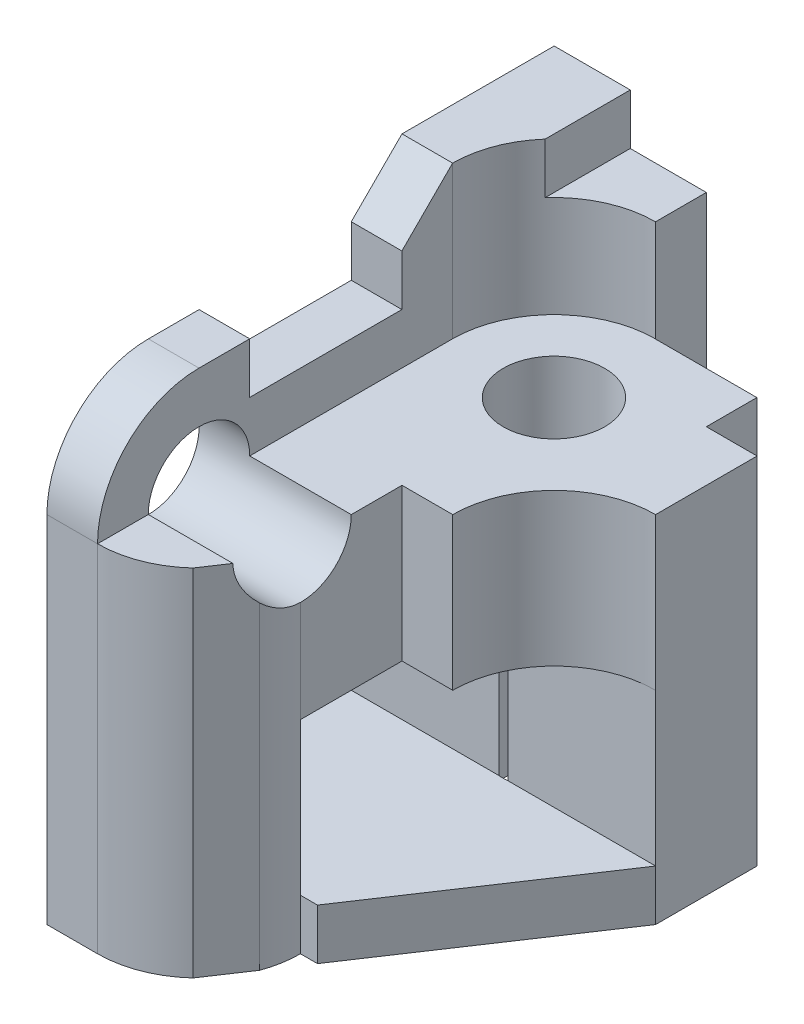
SolidWorks part; units mm, degrees
ref_plane "Front Plane" through (0, 0, 0) normal (0, 0, 1) x (1, 0, 0)
ref_plane "Top Plane" through (0, 0, 0) normal (0, 1, 0) x (1, 0, 0)
ref_plane "Right Plane" through (0, 0, 0) normal (1, 0, 0) x (0, 0, -1)
sketch "Sketch1" plane through (0, 0, 0) normal (0, 0, 1) x (1, 0, 0)
  line L0 (0, 0) -> (0, 7)
  line L1 (0, 7) -> (-3, 7)
  line L2 (-3, 7) -> (-3, 9)
  line L3 (-3, 9) -> (-4.5, 9)
  line L4 (-4.5, 9) -> (-4.5, 10)
  line L5 (-4.5, 10) -> (-6, 10)
  line L6 (-6, 10) -> (-6, 0)
  line L7 (-6, 0) -> (0, 0)
  dimension "D1" = 6
  dimension "D2" = 3
  dimension "D3" = 1.5
  dimension "D4" = 1
  dimension "D5" = 2
  dimension "D6" = 7
extrude "Boss-Extrude1" add sketch "Sketch1" along normal blind 10
sketch "Sketch3" plane through (0, 7, 0) normal (0, 1, 0) x (1, 0, 0)
  line L0 (-3, 0) -> (-3, -1.0041)
  line L1 (-3, -10) -> (-3, 0) construction
  line L2 (-3, -1.0041) -> (-1, -1.0041)
  line L3 (-1, -1.0041) -> (-1, -2)
  line L4 (-1, -2) -> (0, -2)
  line L5 (0, -10) -> (0, 0) construction
  line L6 (0, -2) -> (0, 0)
  line L7 (0, 0) -> (-3, 0)
  dimension "D1" = 1.0041
  dimension "D2" = 2
  dimension "D3" = 1
extrude "Cut-Extrude3" cut sketch "Sketch3" against normal through all
sketch "Sketch5" plane through (0, 7, 0) normal (0, 1, 0) x (1, 0, 0)
  line L0 (-3, -1.0041) -> (-1, -1.0041) construction
  line L1 (-6, -10) -> (-6, 0) construction
  circle A0 centre (-3, -3.0041) radius 1
  point P0 (-3, -3.0041)
  dimension "D3" = 2
  dimension "D1" = 2
  dimension "D2" = 3
extrude "Cut-Extrude5" cut sketch "Sketch5" against normal mid plane 15
sketch "Sketch7" plane through (0, 9, 0) normal (0, 1, 0) x (1, 0, 0)
  line L0 (-3, -2.0041) -> (-3, 0) construction
  line L1 (-3, -1.0021) -> (-3, -2.0041)
  line L2 (-5.0021, -3.0041) -> (-5.0021, -10)
  line L3 (-4.5, -10) -> (-6, -10) construction
  line L4 (-5.0021, -10) -> (-3, -10)
  line L5 (-3, -10) -> (-3, -4.0041)
  arc A0 (-3, -1.0021) -> (-5.0021, -3.0041) centre (-3, -3.0041) ccw
  arc A1 (-3, -4.0041) -> (-3, -2.0041) centre (-3, -3.0041) cw
  arc A2 (-3, -2.0041) -> (-3, -4.0041) centre (-3, -3.0041) ccw construction
  dimension "D1" = 0.9979
extrude "Cut-Extrude7" cut sketch "Sketch7" against normal mid plane 4
sketch "Sketch8" plane through (-6, 0, 0) normal (-1, 0, 0) x (0, 0, 1)
  line L0 (3, 10) -> (4, 9)
  line L1 (10, 10) -> (0, 10) construction
  line L2 (4, 9) -> (4, 8)
  line L3 (4, 8) -> (7, 8)
  line L4 (7, 8) -> (7, 10)
  line L5 (7, 10) -> (3, 10)
  dimension "D1" = 3
  dimension "D2" = 3
  dimension "D3" = 1
  dimension "D4" = 2
  dimension "D5" = 1
extrude "Cut-Extrude10" cut sketch "Sketch8" against normal blind 4
sketch "Sketch9" plane through (-5.0021, 0, 0) normal (1, 0, 0) x (0, 0, -1)
  line L0 (-7, 8) -> (-7, 9)
  line L1 (-7, 8) -> (-7, 10) construction
  line L2 (-7, 9) -> (-8, 9)
  line L3 (-10, 7) -> (-10, 10)
  line L4 (-10, 10) -> (-7, 10)
  line L5 (-7, 10) -> (-7, 9)
  arc A0 (-8, 9) -> (-10, 7) centre (-8, 7) ccw
  circle A1 centre (-8, 7) radius 1
  line M2 (-7, 8) -> (-7, 10)
  line M3 (-7, 10) -> (-10, 10)
  line M4 (-10, 10) -> (-10, 7)
  line M5 (-10, 7) -> (-3.0041, 7)
  dimension "D2" = 2
  dimension "D1" = 1
extrude "Cut-Extrude12" cut sketch "Sketch9" against normal mid plane 14 contours A0 L2 M2 M3 M4 | A1 M5 | A1 M5
sketch "Sketch10" plane through (0, 7, 0) normal (0, 1, 0) x (1, 0, 0)
  line L0 (0, -7) -> (0, -2) construction
  line L1 (-2, -6) -> (-3, -6)
  line L2 (-3, -6) -> (-3, -8.0014)
  line L3 (-3, -8.0014) -> (0, -8)
  line L4 (0, -9) -> (0, -7) construction
  line L5 (0, -8) -> (0, -4)
  line L6 (0, -10) -> (-5.0021, -10) construction
  arc A0 (0, -4) -> (-2, -6) centre (0, -6) ccw
  dimension "D1" = 2
  dimension "D2" = 2
  dimension "D3" = 1
  dimension "D4" = 1.9986
extrude "Cut-Extrude14" cut sketch "Sketch10" against normal blind 6
sketch "Sketch12" plane through (0, 0, 0) normal (1, 0, 0) x (0, 0, -1)
  line L0 (-4, 1) -> (-4, 4)
  line L1 (-4, 1) -> (-4, 7) construction
  line L2 (-4, 4) -> (-8.0014, 4)
  line L3 (-8.0014, 1) -> (-8.0014, 6) construction
  line L4 (-8.0014, 4) -> (-8, 1)
  line L5 (-8, 1) -> (-4, 1)
  dimension "D1" = 3
extrude "Cut-Extrude15" cut sketch "Sketch12" against normal through all
sketch "Sketch18" plane through (0, 0, 0) normal (1, 0, 0) x (0, 0, -1)
  line L0 (-8.0007, 2.5) -> (-10, 2.5)
  line L1 (-8.0014, 4) -> (-8, 1) construction
  line L2 (-10, 0) -> (-10, 7) construction
  line L3 (-10, 2.5) -> (-10, 7)
  line L4 (-10, 7) -> (-8.0007, 7)
  line L5 (-8.0007, 7) -> (-8.0007, 2.5)
extrude "Cut-Extrude29" cut sketch "Sketch18" against normal blind 2
sketch "Sketch21" plane through (0, 0, 8.0007) normal (0, 0, 1) x (1, 0, 0)
  line L0 (0, 6) -> (-1.5, 6)
  line L1 (0, 4) -> (-1.5, 4)
  line L2 (-1.5, 4) -> (-1.5, 6)
  line L3 (0, 6) -> (0, 4)
extrude "Cut-Extrude30" cut sketch "Sketch21" against normal blind 2
sketch "Sketch22" plane through (0, 7, 0) normal (0, 1, 0) x (1, 0, 0)
  line L0 (0, -4) -> (-4, -10)
  line L1 (-2, -10) -> (-5.0021, -10) construction
  line L2 (-4, -10) -> (0, -10)
  line L3 (0, -10) -> (0, -4)
  dimension "D1" = 4
extrude "Cut-Extrude31" cut sketch "Sketch22" against normal blind 7
sketch "Sketch23" plane through (0, 7, 0) normal (0, 1, 0) x (1, 0, 0)
  line L0 (-5.0021, -9) -> (-5.0021, -7) construction
  line L1 (-3.0021, -8) -> (-0.6683, -8)
  line L2 (-0.6683, -8) -> (-0.6683, -10.9871)
  line L3 (-0.6683, -10.9871) -> (-5.1566, -10.9871)
  line L4 (-5.1566, -10.9871) -> (-5.0021, -10)
  arc A0 (-5.0021, -10) -> (-3.0021, -8) centre (-5.0021, -8) ccw
  point P1 (-5.0021, -8)
extrude "Cut-Extrude33" cut sketch "Sketch23" against normal blind 10
sketch "Sketch24" plane through (0, 0, 10) normal (0, 0, 1) x (1, 0, 0)
  line L0 (-5.0021, 0) -> (-5.0021, 7) construction
  point P0 (-5.0021, 3)
  dimension "D1" = 3
sketch3d "3DSketch4"
  spline S0 degree 1 poles (-5.0021, 3, 10) (-5.0021, 3.6757, 3.5544) knots 0 0 1 1
